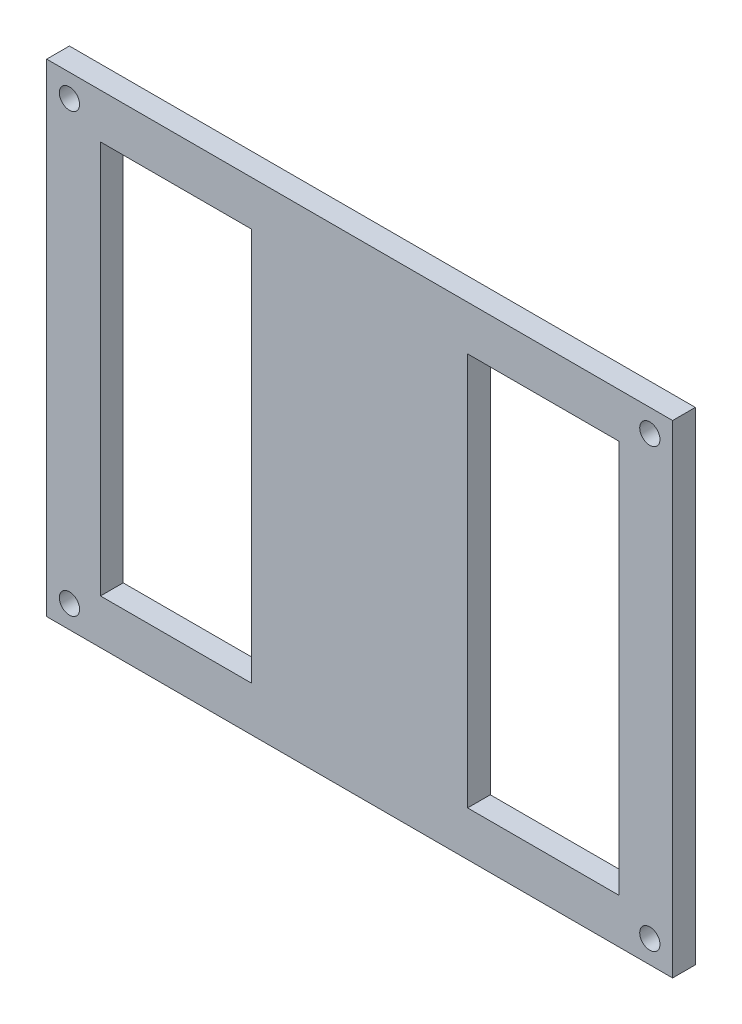
SolidWorks part; units mm, degrees
material "Maple"
ref_plane "Front Plane" through (0, 0, 0) normal (0, 0, 1) x (1, 0, 0)
ref_plane "Top Plane" through (0, 0, 0) normal (0, 1, 0) x (1, 0, 0)
ref_plane "Right Plane" through (0, 0, 0) normal (1, 0, 0) x (0, 0, -1)
sketch "Sketch1" plane through (0, 0, 0) normal (0, 0, 1) x (1, 0, 0)
  line L1 (-50, 40) -> (50, 40)
  line L2 (-50, 40) -> (-50, -40)
  line L3 (-50, -40) -> (50, -40)
  line L4 (50, 40) -> (50, -40)
  line L5 (-50, 40) -> (50, -40) construction
  line L6 (-50, -40) -> (50, 40) construction
  point P0 (0, 0)
  dimension "D1" = 100
  dimension "D2" = 80
extrude "Boss-Extrude1" add sketch "Sketch1" along normal blind 3.175
sketch "Sketch2" plane through (0, 0, 3.175) normal (0, 0, 1) x (1, 0, 0)
  line L0 (-36.3, 32.65) -> (36.3, 32.65) construction
  line L1 (-37.3, 33.65) -> (37.3, 33.65) construction
  line L2 (-37.3, 33.65) -> (-37.3, -33.65) construction
  line L3 (-37.3, -33.65) -> (37.3, -33.65) construction
  line L4 (37.3, 33.65) -> (37.3, -33.65) construction
  line L5 (-37.3, 33.65) -> (37.3, -33.65) construction
  line L6 (-37.3, -33.65) -> (37.3, 33.65) construction
  line L7 (36.3, 32.65) -> (36.3, -32.65) construction
  line L8 (-36.3, -32.65) -> (36.3, -32.65) construction
  line L9 (-36.3, 32.65) -> (-36.3, -32.65) construction
  line L10 (-30.05, 26.4) -> (30.05, 26.4) construction
  line L11 (30.05, 26.4) -> (30.05, -26.4) construction
  line L12 (-30.05, -26.4) -> (30.05, -26.4) construction
  line L13 (-30.05, 26.4) -> (-30.05, -26.4) construction
  line L14 (-36.3, 0) -> (-15, 0) construction
  line L15 (0, 0) -> (0, 10.2165) construction
  line L16 (-36.3, -32.65) -> (-15, -32.65)
  line L17 (-36.3, -32.65) -> (-36.3, 32.65)
  line L18 (-36.3, 32.65) -> (-15, 32.65)
  line L19 (-15, -32.65) -> (-15, 32.65)
  line L20 (-36.3, -32.65) -> (-15, 32.65) construction
  line L21 (-36.3, 32.65) -> (-15, -32.65) construction
  line L22 (36.3, 32.65) -> (15, 32.65)
  line L23 (15, -32.65) -> (15, 32.65)
  line L24 (36.3, -32.65) -> (15, -32.65)
  line L25 (36.3, -32.65) -> (36.3, 32.65)
  line L26 (-36.215, -32.565) -> (-36.215, 32.565)
  line L27 (-36.215, 32.565) -> (-15.085, 32.565)
  line L28 (-15.085, -32.565) -> (-15.085, 32.565)
  line L29 (-36.215, -32.565) -> (-15.085, -32.565)
  line L30 (36.215, 32.565) -> (15.085, 32.565)
  line L31 (15.085, -32.565) -> (15.085, 32.565)
  line L32 (36.215, -32.565) -> (15.085, -32.565)
  line L33 (36.215, -32.565) -> (36.215, 32.565)
  point P0 (0, 0)
  point P17 (-25.65, 0)
  dimension "D1" = 67.3
  dimension "D2" = 74.6
  dimension "D5" = 21.3
  dimension "D3" = 1
  dimension "D4" = 6.25
  dimension "D6" = 0.085
  dimension "D7" = 0.085
sketch "Sketch4" plane through (0, 0, 3.175) normal (0, 0, 1) x (1, 0, 0)
  line L0 (-50.255, 40.255) -> (-50.255, -40.255)
  line L1 (-43.735, 33.735) -> (43.735, 33.735)
  line L2 (-43.735, 33.735) -> (-43.735, -33.735)
  line L3 (-43.735, -33.735) -> (43.735, -33.735)
  line L4 (43.735, 33.735) -> (43.735, -33.735)
  line L5 (-43.735, 33.735) -> (43.735, -33.735) construction
  line L6 (-43.735, -33.735) -> (43.735, 33.735) construction
  line L7 (-50.255, -40.255) -> (50.255, -40.255)
  line L8 (50.255, 40.255) -> (50.255, -40.255)
  line L9 (-50.255, 40.255) -> (50.255, 40.255)
  point P0 (0, 0)
  dimension "D1" = 87.47
  dimension "D2" = 67.47
  dimension "D3" = 6.52
extrude "Cut-Extrude3" cut sketch "Sketch4" against normal blind 10
sketch "Sketch5" plane through (0, 0, 3.175) normal (0, 0, 1) x (1, 0, 0)
  line L0 (-43.735, 33.735) -> (-40.553, 30.553) construction
  line L1 (43.735, 33.735) -> (-43.735, 33.735) construction
  line L2 (0, 0) -> (0, -4.187) construction
  line L3 (0, 0) -> (-6.4708, 0) construction
  circle A0 centre (-40.553, 30.553) radius 1.415
  circle A1 centre (-40.553, -30.553) radius 1.415
  circle A2 centre (40.553, -30.553) radius 1.415
  circle A3 centre (40.553, 30.553) radius 1.415
  dimension "D3" = 2.83
  dimension "D1" = 45
  dimension "D2" = 4.5
extrude "Cut-Extrude4" cut sketch "Sketch5" against normal blind 10
extrude "Cut-Extrude5" cut sketch "Sketch2" against normal blind 10 contours L26 L27 L28 L29 | L30 L31 L32 L33
sketch "Sketch6" plane through (0, 0, 3.175) normal (0, 0, 1) x (1, 0, 0)
  line L0 (-25.65, -32.565) -> (-25.65, -27.475) construction
  line L1 (-36.215, -32.565) -> (-15.085, -32.565) construction
  line L2 (25.65, -32.565) -> (25.65, -27.475) construction
  line L3 (36.215, -32.565) -> (15.085, -32.565) construction
  line L4 (-25.65, -32.565) -> (-15.085, -32.565)
  line L5 (-15.085, -32.565) -> (-15.085, -27.475)
  line L6 (-15.085, -32.565) -> (-15.085, 32.565) construction
  line L7 (-15.085, -27.475) -> (-25.65, -27.475)
  line L8 (-25.65, -27.475) -> (-36.215, -27.475)
  line L9 (-36.215, -32.565) -> (-36.215, 32.565) construction
  line L10 (-36.215, -27.475) -> (-36.215, -32.565)
  line L11 (-36.215, -32.565) -> (-25.65, -32.565)
  line L12 (25.65, -32.565) -> (36.215, -32.565)
  line L13 (36.215, -32.565) -> (36.215, -27.475)
  line L14 (36.215, -32.565) -> (36.215, 32.565) construction
  line L15 (36.215, -27.475) -> (25.65, -27.475)
  line L16 (25.65, -27.475) -> (15.085, -27.475)
  line L17 (15.085, -32.565) -> (15.085, 32.565) construction
  line L18 (15.085, -27.475) -> (15.085, -32.565)
  line L19 (15.085, -32.565) -> (25.65, -32.565)
  line L20 (0, 0) -> (17.3086, 0) construction
  line L21 (15.085, 27.475) -> (15.085, 32.565)
  line L22 (25.65, 27.475) -> (15.085, 27.475)
  line L23 (36.215, 27.475) -> (25.65, 27.475)
  line L24 (36.215, 32.565) -> (36.215, 27.475)
  line L25 (25.65, 32.565) -> (36.215, 32.565)
  line L26 (15.085, 32.565) -> (25.65, 32.565)
  line L27 (-36.215, 27.475) -> (-36.215, 32.565)
  line L28 (-25.65, 27.475) -> (-36.215, 27.475)
  line L29 (-15.085, 27.475) -> (-25.65, 27.475)
  line L30 (-15.085, 32.565) -> (-15.085, 27.475)
  line L31 (-25.65, 32.565) -> (-15.085, 32.565)
  line L32 (-36.215, 32.565) -> (-25.65, 32.565)
  dimension "D1" = 5.09
  dimension "D2" = 5.09
extrude "Boss-Extrude2" add sketch "Sketch6" against normal blind 3.175
equation "\"length\"=100"
equation "\"D1@Sketch1\"=\"length\" "
equation "\"width\"=80"
equation "\"D2@Sketch1\"=\"width\""
equation "\"depth\"=3.175"
equation "\"D1@Boss-Extrude1\"= \"depth\""
equation "\"D1@Sketch2\"=\"width\"-4*\"depth\""
equation "\"kerf\"= 0.17 / 2"
equation "\"D3@Sketch5\"= 3.00mm - 2*\"kerf\""
equation "\"D2@Sketch4\"= 67.30mm + 2*\"kerf\""
equation "\"D1@Sketch4\"= 87.30mm + 2*\"kerf\""
equation "\"D3@Sketch4\"= 6.35mm + 2*\"kerf\""
equation "\"D5@Sketch2\"=21.30mm"
